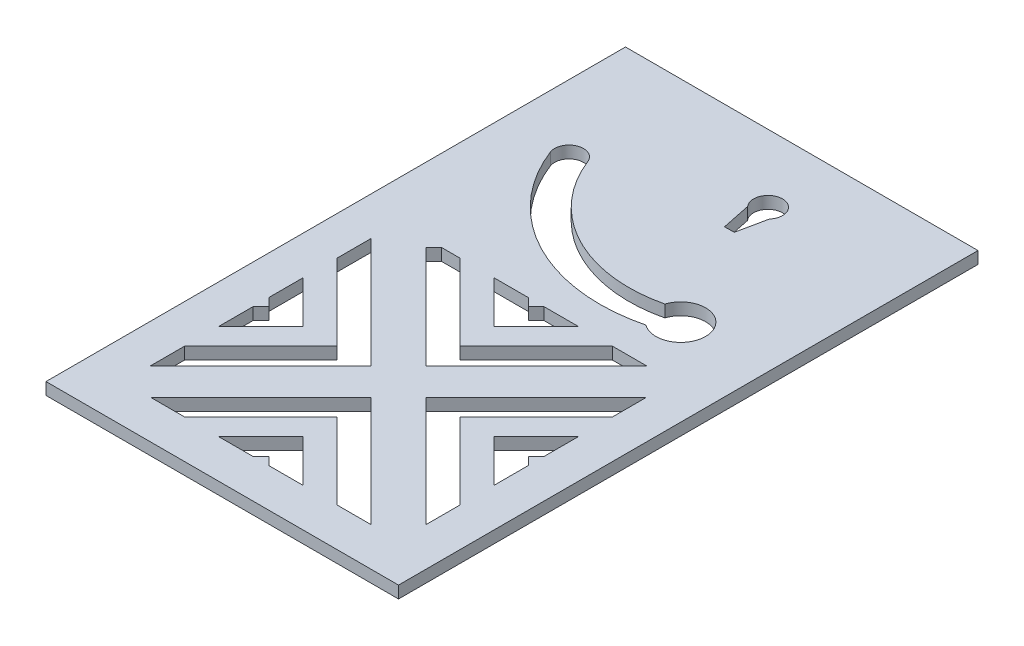
SolidWorks part; units mm, degrees
ref_plane "Ön Düzlem" through (0, 0, 0) normal (0, 0, 1) x (1, 0, 0)
ref_plane "Üst Düzlem" through (0, 0, 0) normal (0, 1, 0) x (1, 0, 0)
ref_plane "Sağ Düzlem" through (0, 0, 0) normal (1, 0, 0) x (0, 0, -1)
sketch "Çizim1" plane through (0, 0, 0) normal (0, 1, 0) x (1, 0, 0)
  line L1 (0, 0) -> (73, 0)
  line L2 (0, 0) -> (0, 120)
  line L3 (0, 120) -> (73, 120)
  line L4 (73, 0) -> (73, 120)
  dimension "D1" = 73
  dimension "D2" = 120
extrude "Yükseklik-Ekstrüzyon1" add sketch "Çizim1" along normal blind 2.5
sketch "Çizim4" plane through (0, 0, 0) normal (0, -1, 0) x (1, 0, 0)
  line L0 (41.2584, -104.027) -> (42.5001, -98.0091)
  line L1 (45.7584, -104.046) -> (44.4999, -98.0315)
  line L2 (42.5001, -98.0091) -> (44.4999, -98.0315)
  line L8 (0, 0) -> (0, -120)
  line L9 (0, -120) -> (73, -120)
  line L10 (73, -120) -> (73, 0)
  line L11 (73, 0) -> (0, 0)
  line L12 (0, 0) -> (0, -120)
  line L13 (0, -120) -> (73, -120)
  line L14 (73, -120) -> (73, 0)
  line L15 (73, 0) -> (0, 0)
  arc A0 (41.2584, -104.027) -> (45.7584, -104.046) centre (43.5, -106.0208) ccw
  point P8 (43.5, -98.0203)
  dimension "D4" = 3
  dimension "D1" = 8
  dimension "D2" = 0
  dimension "D3" = 2
  dimension "D5" = 4.5
  dimension "D6" = 6
extrude "Kes-Ekstrüzyon2" cut sketch "Çizim4" against normal through all contours A0
sketch "Çizim5" plane through (0, 0, 0) normal (0, -1, 0) x (1, 0, 0)
  circle A0 centre (55.0654, -76.377) radius 3
  circle A1 centre (13.8563, -94.4554) radius 3
  arc A2 (55.0654, -76.377) -> (13.8563, -94.4554) centre (43.5, -106.0208) ccw construction
  arc A3 (56.1558, -73.5822) -> (11.0614, -93.365) centre (43.5, -106.0208) ccw
  arc A4 (53.975, -79.1719) -> (16.6511, -95.5458) centre (43.5, -106.0208) ccw
  arc A5 (53.975, -79.1719) -> (56.1558, -73.5822) centre (55.0654, -76.377) ccw
  arc A6 (11.0614, -93.365) -> (16.6511, -95.5458) centre (13.8563, -94.4554) ccw
  point P9 (30.7167, -76.8815)
  dimension "D1" = 6
  dimension "D2" = 6
extrude "Kes-Ekstrüzyon3" cut sketch "Çizim5" against normal through all contours A1 | A4 A0 A3 A1 | A0
sketch "Çizim6" plane through (0, 0, 0) normal (0, -1, 0) x (1, 0, 0)
  circle A0 centre (55.0654, -76.377) radius 5.15
  dimension "D1" = 10.3
extrude "Kes-Ekstrüzyon4" cut sketch "Çizim6" against normal through all
sketch "Çizim7" plane through (0, 0, 0) normal (0, -1, 0) x (1, 0, 0)
  line L0 (65, -65) -> (65, -8)
  line L1 (65, -8) -> (8, -8)
  line L2 (8, -8) -> (8, -65)
  line L3 (8, -65) -> (65, -65)
  line L4 (0, 0) -> (0, -120)
  line L5 (0, -120) -> (73, -120)
  line L6 (73, -120) -> (73, 0)
  line L7 (73, 0) -> (0, 0)
  line L11 (73, 0) -> (0, 0)
  line L12 (8, -8) -> (8, -120) construction
  line L13 (73, -120) -> (73, 0) construction
  line L14 (65, -120) -> (65, -8) construction
  line L15 (0, 0) -> (0, -120) construction
  line L16 (8, -65) -> (65, -8) construction
  line L17 (8, -8) -> (65, -65) construction
  line L18 (52.2721, -65) -> (32.9645, -45.6924)
  line L19 (29.4289, -49.2279) -> (45.201, -65)
  line L20 (25.8934, -52.7635) -> (38.1299, -65)
  line L21 (13.6569, -65) -> (36.5, -42.1569)
  line L22 (20.7279, -65) -> (40.0355, -45.6924)
  line L23 (27.799, -65) -> (43.5711, -49.2279)
  line L24 (34.8701, -65) -> (47.1066, -52.7635)
  line L25 (22.3579, -56.299) -> (31.0589, -65)
  line L26 (41.9411, -65) -> (50.6421, -56.299)
  line L27 (49.0122, -65) -> (54.1777, -59.8345)
  line L28 (56.0833, -65) -> (57.7132, -63.3701)
  line L29 (23.9878, -65) -> (18.8223, -59.8345)
  line L30 (16.9167, -65) -> (15.2868, -63.3701)
  line L31 (8, -16.9167) -> (9.6299, -15.2868)
  line L32 (36.5, -42.1569) -> (59.3431, -65)
  line L33 (8, -13.6569) -> (30.8431, -36.5)
  line L34 (8, -23.9878) -> (13.1655, -18.8223)
  line L35 (8, -20.7279) -> (27.3076, -40.0355)
  line L36 (16.701, -22.3579) -> (8, -31.0589)
  line L37 (20.2365, -25.8934) -> (8, -38.1299)
  line L38 (23.7721, -29.4289) -> (8, -45.201)
  line L39 (8, -52.2721) -> (27.3076, -32.9645)
  line L40 (30.8431, -36.5) -> (8, -59.3431)
  line L41 (8, -27.799) -> (23.7721, -43.5711)
  line L42 (8, -34.8701) -> (20.2365, -47.1066)
  line L43 (8, -41.9411) -> (16.701, -50.6421)
  line L44 (8, -49.0122) -> (13.1655, -54.1777)
  line L45 (56.0833, -8) -> (57.7132, -9.6299)
  line L46 (59.3431, -8) -> (36.5, -30.8431)
  line L47 (49.0122, -8) -> (54.1777, -13.1655)
  line L48 (52.2721, -8) -> (32.9645, -27.3076)
  line L49 (50.6421, -16.701) -> (41.9411, -8)
  line L50 (47.1066, -20.2365) -> (34.8701, -8)
  line L51 (43.5711, -23.7721) -> (27.799, -8)
  line L52 (20.7279, -8) -> (40.0355, -27.3076)
  line L53 (36.5, -30.8431) -> (13.6569, -8)
  line L54 (45.201, -8) -> (29.4289, -23.7721)
  line L55 (38.1299, -8) -> (25.8934, -20.2365)
  line L56 (31.0589, -8) -> (22.3579, -16.701)
  line L57 (23.9878, -8) -> (18.8223, -13.1655)
  line L58 (65, -56.0833) -> (63.3701, -57.7132)
  line L59 (65, -59.3431) -> (42.1569, -36.5)
  line L60 (65, -49.0122) -> (59.8345, -54.1777)
  line L61 (65, -52.2721) -> (45.6924, -32.9645)
  line L62 (56.299, -50.6421) -> (65, -41.9411)
  line L63 (52.7635, -47.1066) -> (65, -34.8701)
  line L64 (49.2279, -43.5711) -> (65, -27.799)
  line L65 (65, -20.7279) -> (45.6924, -40.0355)
  line L66 (42.1569, -36.5) -> (65, -13.6569)
  line L67 (65, -45.201) -> (49.2279, -29.4289)
  line L68 (65, -38.1299) -> (52.7635, -25.8934)
  line L69 (65, -31.0589) -> (56.299, -22.3579)
  line L70 (65, -23.9878) -> (59.8345, -18.8223)
  point P38 (36.5, -36.5)
  point P44 (36.5, -36.5)
  point P117 (36.5, -36.5)
  dimension "D3" = 4
  dimension "D4" = 4
  dimension "D5" = 5
  dimension "D6" = 5
  dimension "D7" = 5
  dimension "D8" = 5
  dimension "D9" = 5
  dimension "D10" = 5
  dimension "D11" = 5
  dimension "D12" = 5
  dimension "D13" = 5
  dimension "D14" = 5
  dimension "D15" = 5
  dimension "D16" = 5
  dimension "D1" = 0
  dimension "D2" = 8
  dimension "D17" = 4
extrude "Kes-Ekstrüzyon5" cut sketch "Çizim7" against normal through all contours L30 L3 L22 L29 L21 | L29 L22 L25 L21 | L21 L25 L22 L20 | L20 L22 L19 L21 | L19 L22 L18 L21 | L32 L21 L18 L22 | L32 L22 L18 L23 | L32 L23 L18 L24 | L32 L24 L18 L26 | L32 L26 L18 L27 | L32 L27 L18 L3 L28 | L32 L28 L3 | L26 L3 L19 | L3 L26 L19 L24 L20 | L20 L24 L19 L23 | L23 L25 L3 L24 L20 | L25 L23 L3 | L44 L39 L2 L40 | L39 L44 L40 L43 | L39 L43 L40 L42 | L39 L42 L40 L41 | L39 L41 L40 L35 | L40 L33 L39 L35 | L35 L39 L33 L38 | L38 L33 L37 L35 | L37 L33 L36 L35 | L36 L33 L34 L35 | L2 L35 L34 L33 L31 | L33 L2 L31 | L43 L2 L38 | L2 L43 L38 L42 L37 | L37 L42 L38 L41 | L2 L42 L37 L41 L36 | L41 L2 L36 | L59 L0 L58 | L0 L61 L60 L59 L58 | L62 L59 L60 L61 | L63 L59 L62 L61 | L64 L59 L63 L61 | L61 L65 L59 L64 | L66 L59 L65 L61 | L65 L67 L66 L61 | L65 L68 L66 L67 | L65 L69 L66 L68 | L65 L70 L66 L69 | L70 L65 L0 L66 | L63 L68 L64 L67 | L0 L68 L63 L67 L62 | L0 L69 L64 L68 L63 | L69 L0 L64 | L67 L0 L62 | L57 L52 L1 L53 | L52 L57 L53 L56 | L52 L56 L53 L55 | L52 L55 L53 L54 | L52 L54 L53 L48 | L48 L52 L46 L51 | L51 L46 L50 L48 | L50 L46 L49 L48 | L49 L46 L47 L48 | L1 L48 L47 L46 L45 | L1 L55 L50 L54 L49 | L50 L55 L51 L54 | L1 L56 L51 L55 L50 | L46 L1 L45 | L56 L1 L51 | L53 L46 L52 L48 | L54 L1 L49
